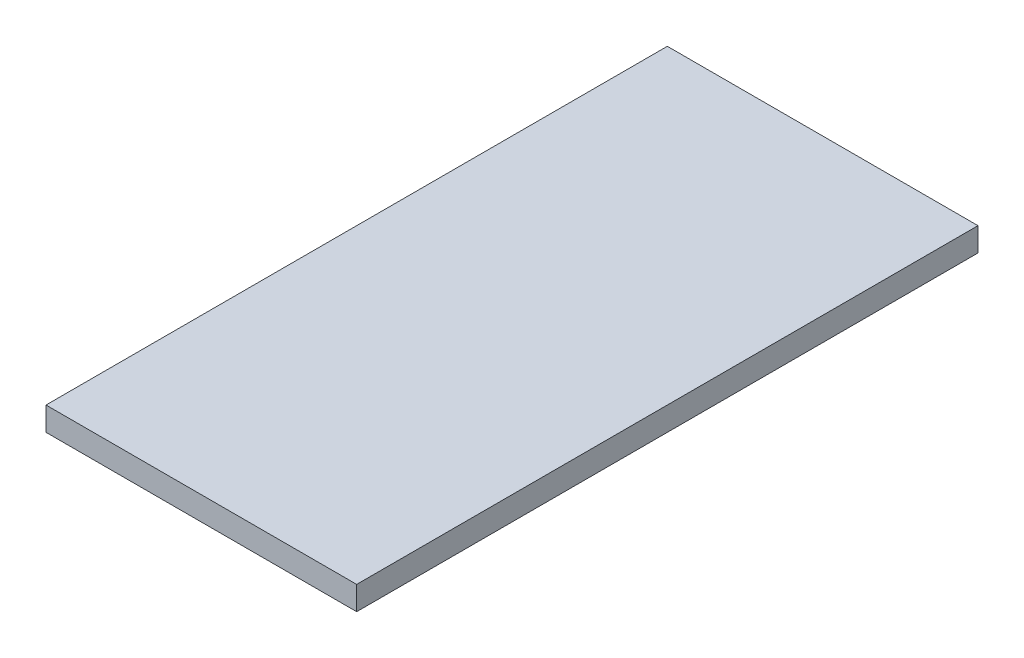
SolidWorks part; units mm, degrees
material "Nylon 6/10"
ref_plane "Front Plane" through (0, 0, 0) normal (0, 0, 1) x (1, 0, 0)
ref_plane "Top Plane" through (0, 0, 0) normal (0, 1, 0) x (1, 0, 0)
ref_plane "Right Plane" through (0, 0, 0) normal (1, 0, 0) x (0, 0, -1)
sketch "Sketch1" plane through (0, 0, 0) normal (0, 1, 0) x (1, 0, 0)
  line L1 (-6.35, 12.7) -> (6.35, 12.7)
  line L2 (-6.35, 12.7) -> (-6.35, -12.7)
  line L3 (-6.35, -12.7) -> (6.35, -12.7)
  line L4 (6.35, 12.7) -> (6.35, -12.7)
  line L5 (-6.35, 12.7) -> (6.35, -12.7) construction
  line L6 (-6.35, -12.7) -> (6.35, 12.7) construction
  point P0 (0, 0)
  dimension "D1" = 12.7
  dimension "D2" = 25.4
extrude "Boss-Extrude1" add sketch "Sketch1" along normal blind 0.9677
